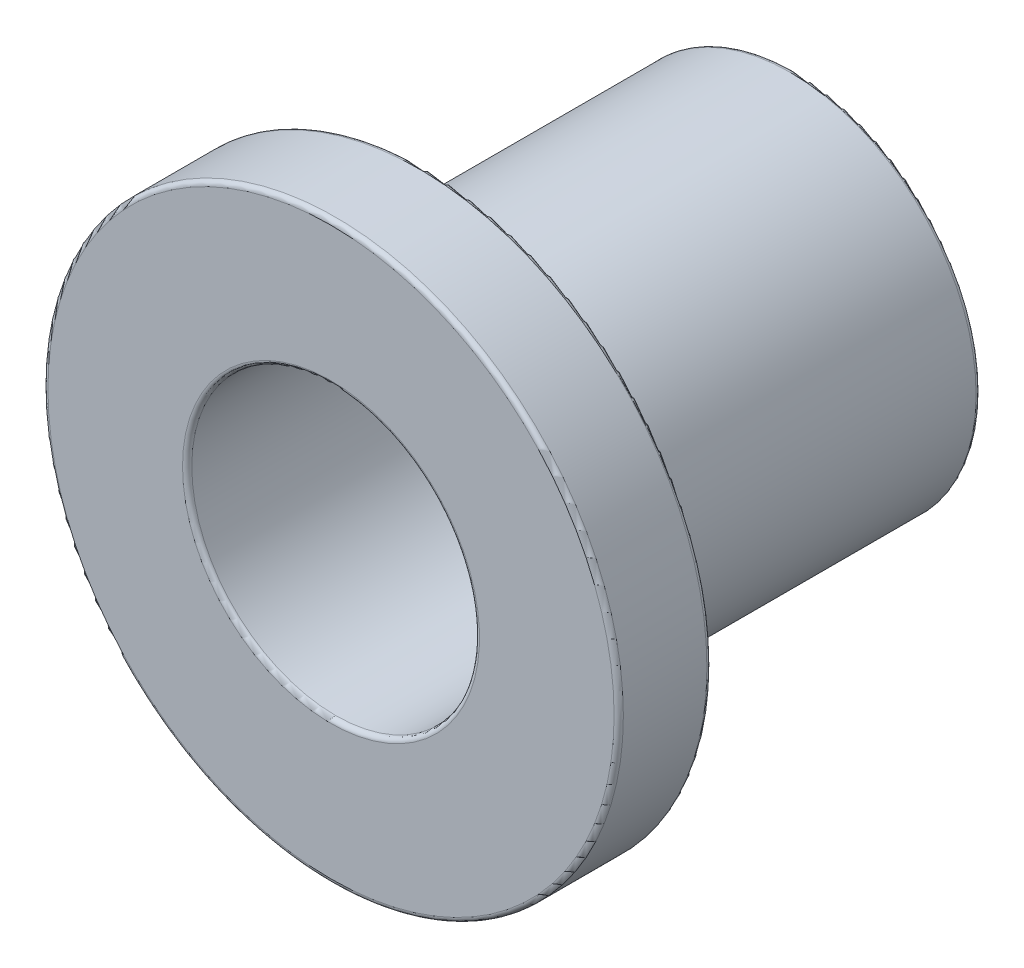
SolidWorks part; units mm, degrees
ref_plane "Front Plane" through (0, 0, 0) normal (0, 0, 1) x (1, 0, 0)
ref_plane "Top Plane" through (0, 0, 0) normal (0, 1, 0) x (1, 0, 0)
ref_plane "Right Plane" through (0, 0, 0) normal (1, 0, 0) x (0, 0, -1)
sketch "Sketch1" plane through (0, 0, 0) normal (-1, 0, 0) x (0, 0, 1)
  line L0 (2.5, 1.55) -> (-2.5, 1.55)
  line L1 (-2.5, 1.55) -> (-2.5, 2)
  line L2 (-2.5, 2) -> (1.5, 2)
  line L3 (1.5, 2) -> (1.5, 3.1)
  line L4 (1.5, 3.1) -> (2.5, 3.1)
  line L6 (2.5, 3.1) -> (2.5, 1.55)
  line L7 (2.5, 0) -> (-2.5, 0) construction
  dimension "ID" = 3.1
  dimension "OD" = 6.2
  dimension "Sleeve OD" = 4
  dimension "Thickness" = 1
  dimension "Overall Height" = 5
sketch "Sketch2" plane through (0, 0, 0) normal (1, 0, 0) x (0, 0, -1)
  line L6 (-2.5, 1.55) -> (2.5, 1.55)
  line L7 (2.5, 1.55) -> (2.5, 2)
  line L8 (2.5, 2) -> (-1.5, 2)
  line L9 (-1.5, 2) -> (-1.5, 3.1)
  line L10 (-1.5, 3.1) -> (-2.5, 3.1)
  line L11 (-2.5, 3.1) -> (-2.5, 1.55)
  line L12 (-2.5, 1.55) -> (2.5, 1.55)
  line L13 (2.5, 1.55) -> (2.5, 2)
  line L14 (2.5, 2) -> (-1.5, 2)
  line L15 (-1.5, 2) -> (-1.5, 3.1)
  line L16 (-1.5, 3.1) -> (-2.5, 3.1)
  line L17 (-2.5, 3.1) -> (-2.5, 1.55)
  dimension "D1" = 0
revolve "Revolve1" add sketch "Sketch2" angle 360 about L7
fillet "Fillet1" radius 0.05 6 edges at (1.55, 0, 2.5) (1.55, 0, -2.5) (2, 0, -2.5) (2, 0, 1.5) (3.1, 0, 1.5) (3.1, 0, 2.5)
equation "\"D1@Fillet1\"=\"Thickness@Sketch1\"*0.05"
